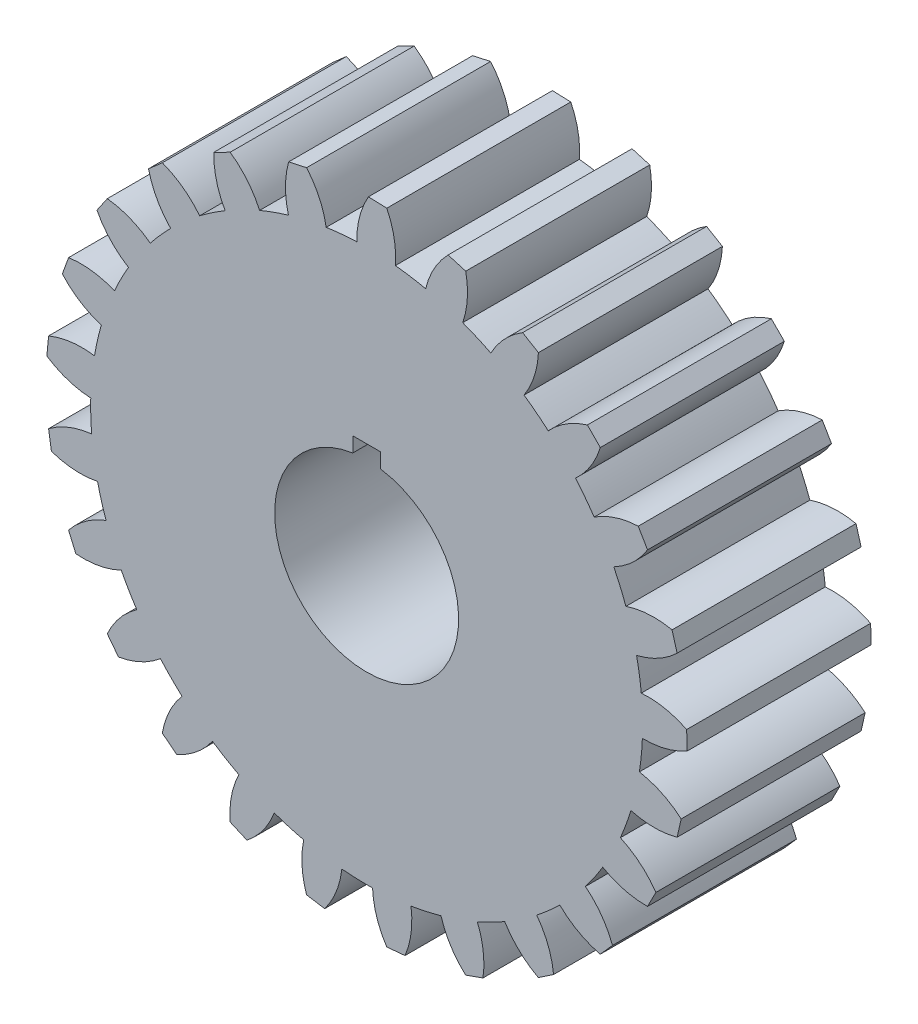
SolidWorks part; units mm, degrees
ref_plane "Front Plane" through (0, 0, 0) normal (0, 0, 1) x (1, 0, 0)
ref_plane "Top Plane" through (0, 0, 0) normal (0, 1, 0) x (1, 0, 0)
ref_plane "Right Plane" through (0, 0, 0) normal (1, 0, 0) x (0, 0, -1)
sketch "Sketch1" plane through (0, 0, 0) normal (0, 0, 1) x (1, 0, 0)
  circle A0 centre (0, 0) radius 152.4
extrude "Boss-Extrude1" add sketch "Sketch1" along normal blind 101.6
sketch "Sketch2" plane through (0, 0, 101.6) normal (0, 0, 1) x (1, 0, 0)
  line L2 (-7.62, 50.2252) -> (-7.62, 58.42)
  line L3 (-7.62, 58.42) -> (7.62, 58.42)
  line L4 (7.62, 50.2252) -> (7.62, 58.42)
  line L5 (0, 50.8) -> (7.62, 58.42) construction
  line L6 (-7.62, 58.42) -> (-0.0706, 50.8706) construction
  arc A0 (-7.62, 50.2252) -> (7.62, 50.2252) centre (0, 0) ccw
  point P3 (0, 50.8)
  dimension "D1" = 15.24
extrude "Cut-Extrude1" cut sketch "Sketch2" against normal through all
sketch "Sketch3" plane through (0, 0, 101.6) normal (0, 0, 1) x (1, 0, 0)
  line L0 (5.2209, 152.3105) -> (6.0946, 177.8) construction
  line L1 (0.9846, 177.0111) -> (11.1386, 176.663)
  line L2 (44.9745, 171.2051) -> (54.723, 168.3428)
  line L3 (86.1385, 154.6417) -> (94.8689, 149.4449)
  line L4 (121.8901, 128.3616) -> (129.0539, 121.1569)
  line L5 (149.983, 94.016) -> (155.1299, 85.2562)
  line L6 (168.6518, 53.7631) -> (171.4585, 43.9984)
  line L7 (176.7236, 10.132) -> (177.0138, -0.0239)
  line L8 (173.6912, -34.1357) -> (171.4467, -44.0447)
  line L9 (159.7452, -76.2585) -> (155.1069, -85.298)
  line L10 (135.7618, -113.5897) -> (129.0212, -121.1917)
  line L11 (103.248, -143.7837) -> (94.8286, -149.4705)
  line L12 (64.2467, -164.9432) -> (54.6776, -168.3575)
  line L13 (21.2086, -175.7387) -> (11.091, -176.666)
  line L14 (-23.1622, -175.4919) -> (-33.1925, -173.874)
  line L15 (-66.0775, -164.2183) -> (-75.3904, -160.1567)
  line L16 (-104.841, -142.6263) -> (-112.8512, -136.3763)
  line L17 (-137.017, -112.0725) -> (-143.2212, -104.0268)
  line L18 (-160.5836, -74.4768) -> (-164.5921, -65.141)
  line L19 (-174.0602, -32.2014) -> (-175.621, -22.162)
  line L20 (-176.6, 12.0972) -> (-175.615, 22.2094)
  line L21 (-168.0433, 55.6358) -> (-164.5745, 65.1853)
  line L22 (-148.9278, 95.6786) -> (-143.1932, 104.0654)
  line L23 (-120.4547, 129.7095) -> (-112.8145, 136.4067)
  line L24 (-84.413, 155.5903) -> (-75.3472, 160.1771)
  line L25 (-43.0672, 171.6948) -> (-33.1457, 173.8829)
  line L26 (0, 0) -> (15.8696, 151.5715) construction
  arc A1 (15.8696, 151.5715) -> (-5.4535, 152.3024) centre (0, 0) ccw
  arc A2 (15.8696, 151.5715) -> (11.1386, 176.663) centre (-32.1489, 155.5094) ccw
  arc A3 (-5.4535, 152.3024) -> (0.9846, 177.0111) centre (42.7219, 152.943) cw
  arc A4 (53.0653, 142.863) -> (54.723, 168.3428) centre (7.5348, 158.6189) ccw
  arc A5 (53.0653, 142.863) -> (32.5939, 148.8738) centre (0, 0) ccw
  arc A6 (32.5939, 148.8738) -> (44.9745, 171.2051) centre (79.4151, 137.5135) cw
  arc A7 (86.9268, 125.1779) -> (94.8689, 149.4449) centre (46.7449, 151.7618) ccw
  arc A8 (86.9268, 125.1779) -> (68.5933, 136.0908) centre (0, 0) ccw
  arc A9 (68.5933, 136.0908) -> (86.1385, 154.6417) centre (111.1184, 113.4435) cw
  arc A10 (115.3263, 99.6274) -> (129.0539, 121.1569) centre (83.018, 135.3689) ccw
  arc A11 (115.3263, 99.6274) -> (100.2827, 114.7568) centre (0, 0) ccw
  arc A12 (100.2827, 114.7568) -> (121.8901, 128.3616) centre (135.8396, 82.2455) cw
  arc A13 (136.4794, 67.8169) -> (155.1299, 85.2562) centre (114.0747, 110.4703) ccw
  arc A14 (136.4794, 67.8169) -> (125.671, 86.2122) centre (0, 0) ccw
  arc A15 (125.671, 86.2122) -> (149.983, 94.016) centre (152.0256, 45.8796) cw
  arc A16 (149.057, 31.7453) -> (171.4585, 43.9984) centre (137.9637, 78.6304) ccw
  arc A17 (149.057, 31.7453) -> (143.163, 52.2506) centre (0, 0) ccw
  arc A18 (143.163, 52.2506) -> (168.6518, 53.7631) centre (158.6592, 6.631) cw
  arc A19 (152.2689, -6.321) -> (177.0138, -0.0239) centre (153.1839, 41.85) ccw
  arc A20 (152.2689, -6.321) -> (151.6594, 15.0059) centre (0, 0) ccw
  arc A21 (151.6594, 15.0059) -> (176.7236, 10.132) centre (155.3237, -33.0343) cw
  arc A22 (145.9131, -43.9902) -> (171.4467, -44.0447) centre (158.779, 2.4399) ccw
  arc A23 (145.9131, -43.9902) -> (150.6266, -23.1817) centre (0, 0) ccw
  arc A24 (150.6266, -23.1817) -> (173.6912, -34.1357) centre (142.2287, -70.6239) cw
  arc A25 (130.389, -78.8952) -> (155.1069, -85.298) centre (154.3974, -37.1235) ccw
  arc A26 (130.389, -78.8952) -> (140.1293, -59.9127) centre (0, 0) ccw
  arc A27 (140.1293, -59.9127) -> (159.7452, -76.2585) centre (120.1968, -103.7759) cw
  arc A28 (106.6722, -108.843) -> (129.0212, -121.1917) centre (140.3145, -74.3543) ccw
  arc A29 (106.6722, -108.843) -> (120.8272, -92.8792) centre (0, 0) ccw
  arc A30 (120.8272, -92.8792) -> (135.7618, -113.5897) centre (90.6126, -130.4073) cw
  arc A31 (76.2527, -131.9518) -> (94.8286, -149.4705) centre (117.4151, -106.9131) ccw
  arc A32 (76.2527, -131.9518) -> (93.9331, -120.0097) centre (0, 0) ccw
  arc A33 (93.9331, -120.0097) -> (103.248, -143.7837) centre (55.3349, -148.8448) cw
  arc A34 (41.042, -146.7696) -> (54.6776, -168.3575) centre (87.1381, -132.7542) ccw
  arc A35 (41.042, -146.7696) -> (61.1368, -139.5996) centre (0, 0) ccw
  arc A36 (61.1368, -139.5996) -> (64.2467, -164.9432) centre (16.5802, -157.9298) cw
  arc A37 (3.2525, -152.3653) -> (11.091, -176.666) centre (51.3859, -150.2538) ccw
  arc A38 (3.2525, -152.3653) -> (24.499, -150.4179) centre (0, 0) ccw
  arc A39 (24.499, -150.4179) -> (21.2086, -175.7387) centre (-23.2162, -157.0915) cw
  arc A40 (-34.7414, -148.3873) -> (-33.1925, -173.874) centre (12.4049, -158.3125) ccw
  arc A41 (-34.7414, -148.3873) -> (-13.6781, -151.7849) centre (0, 0) ccw
  arc A42 (-13.6781, -151.7849) -> (-23.1622, -175.4919) centre (-61.5539, -146.3825) cw
  arc A43 (-70.5524, -135.0856) -> (-75.3904, -160.1567) centre (-27.3556, -156.4238) ccw
  arc A44 (-70.5524, -135.0856) -> (-50.9957, -143.6147) centre (0, 0) ccw
  arc A45 (-50.9957, -143.6147) -> (-66.0775, -164.2183) centre (-96.0239, -126.4758) cw
  arc A46 (-101.9303, -113.296) -> (-112.8512, -136.3763) centre (-65.3971, -144.7064) ccw
  arc A47 (-101.9303, -113.296) -> (-85.1091, -126.4207) centre (0, 0) ccw
  arc A48 (-85.1091, -126.4207) -> (-104.841, -142.6263) centre (-124.4604, -98.6222) cw
  arc A49 (-126.9035, -84.3876) -> (-143.2212, -104.0268) centre (-99.3296, -123.8966) ccw
  arc A50 (-126.9035, -84.3876) -> (-113.8748, -101.2832) centre (0, 0) ccw
  arc A51 (-113.8748, -101.2832) -> (-137.017, -112.0725) centre (-145.0766, -64.5717) cw
  arc A52 (-143.9029, -50.1768) -> (-164.5921, -65.141) centre (-127.0208, -95.3019) ccw
  arc A53 (-143.9029, -50.1768) -> (-135.4853, -69.7817) centre (0, 0) ccw
  arc A54 (-135.4853, -69.7817) -> (-160.5836, -74.4768) centre (-156.5771, -26.464) cw
  arc A55 (-151.8604, -12.8132) -> (-175.621, -22.162) centre (-146.7308, -60.719) ccw
  arc A56 (-151.8604, -12.8132) -> (-148.5828, -33.8955) centre (0, 0) ccw
  arc A57 (-148.5828, -33.8955) -> (-174.0602, -32.2014) centre (-158.2392, 13.3066) cw
  arc A58 (-150.2759, 25.3555) -> (-175.615, 22.2094) centre (-157.2212, -22.3209) ccw
  arc A59 (-150.2759, 25.3555) -> (-152.3443, 4.1204) centre (0, 0) ccw
  arc A60 (-152.3443, 4.1204) -> (-176.6, 12.0972) centre (-149.9587, 52.241) cw
  arc A61 (-139.2491, 61.9311) -> (-164.5745, 65.1853) centre (-157.8328, 17.4796) ccw
  arc A62 (-139.2491, 61.9311) -> (-146.5334, 41.8775) centre (0, 0) ccw
  arc A63 (-146.5334, 41.8775) -> (-168.0433, 55.6358) centre (-132.2556, 87.893) cw
  arc A64 (-119.4727, 94.6152) -> (-143.1932, 104.0654) centre (-148.5272, 56.1819) ccw
  arc A65 (-119.4727, 94.6152) -> (-131.5153, 77.0032) centre (0, 0) ccw
  arc A66 (-131.5153, 77.0032) -> (-148.9278, 95.6786) centre (-106.2425, 118.0223) cw
  arc A67 (-92.1894, 121.3544) -> (-112.8145, 136.4067) centre (-129.889, 91.354) ccw
  arc A68 (-92.1894, 121.3544) -> (-108.2336, 107.2905) centre (0, 0) ccw
  arc A69 (-108.2336, 107.2905) -> (-120.4547, 129.7095) centre (-73.5537, 140.7358) cw
  arc A70 (-59.1135, 140.4683) -> (-75.3472, 160.1771) centre (-103.0895, 120.7861) ccw
  arc A71 (-59.1135, 140.4683) -> (-78.1512, 130.8364) centre (0, 0) ccw
  arc A72 (-78.1512, 130.8364) -> (-84.413, 155.5903) centre (-36.2433, 154.6064) cw
  arc A73 (-22.3233, 150.7562) -> (-33.1457, 173.8829) centre (-69.8125, 142.6287) ccw
  arc A74 (-22.3233, 150.7562) -> (-43.1582, 146.1613) centre (0, 0) ccw
  arc A75 (-43.1582, 146.1613) -> (-43.0672, 171.6948) centre (3.3444, 158.7625) cw
  dimension "D3" = 152.4
  dimension "D2" = 5.08
  dimension "D1" = 177.8
extrude "Boss-Extrude3" add sketch "Sketch3" against normal blind 101.6
